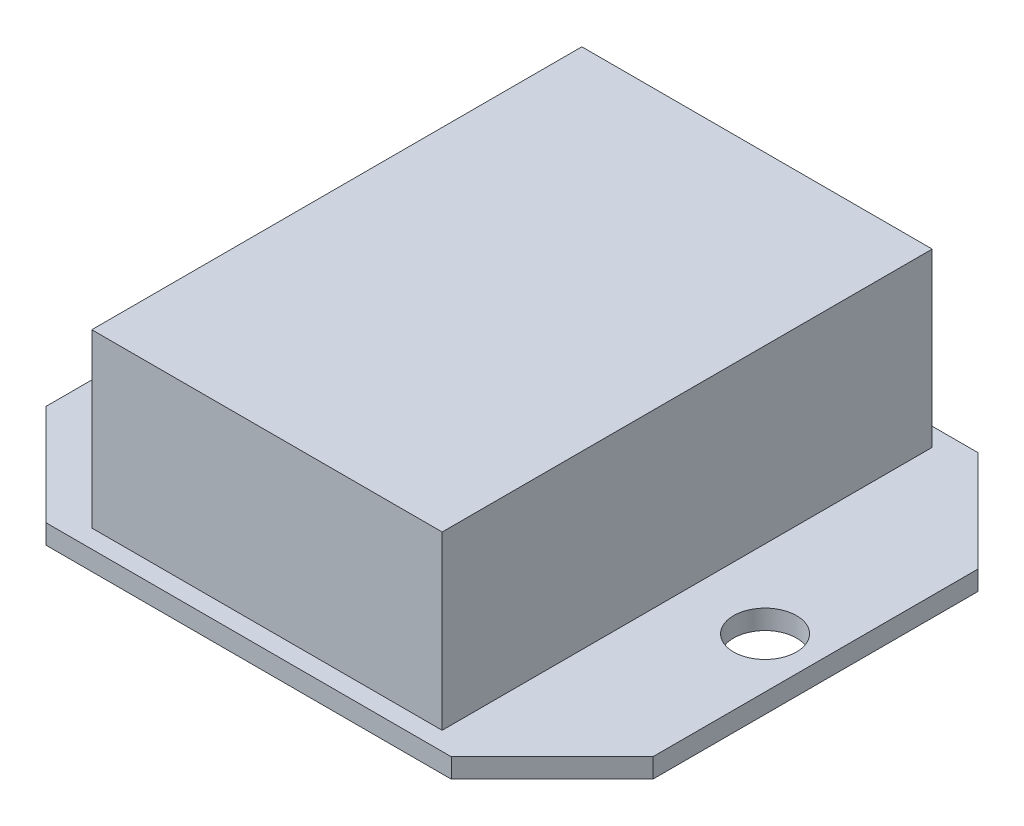
SolidWorks part; units mm, degrees
ref_plane "Front Plane" through (0, 0, 0) normal (0, 0, 1) x (1, 0, 0)
ref_plane "Top Plane" through (0, 0, 0) normal (0, 1, 0) x (1, 0, 0)
ref_plane "Right Plane" through (0, 0, 0) normal (1, 0, 0) x (0, 0, -1)
sketch "Sketch1" plane through (0, 0, 0) normal (0, 1, 0) x (1, 0, 0)
  line L1 (-33.655, 29.21) -> (33.655, 29.21)
  line L2 (-33.655, 29.21) -> (-33.655, -29.21)
  line L3 (-33.655, -29.21) -> (33.655, -29.21)
  line L4 (33.655, 29.21) -> (33.655, -29.21)
  line L5 (-33.655, 29.21) -> (33.655, -29.21) construction
  line L6 (-33.655, -29.21) -> (33.655, 29.21) construction
  point P0 (0, 0)
  dimension "D1" = 67.31
  dimension "D2" = 58.42
extrude "Boss-Extrude1" add sketch "Sketch1" along normal blind 2.159
sketch "Sketch2" plane through (0, 2.159, 0) normal (0, 1, 0) x (1, 0, 0)
  line L5 (33.655, 29.21) -> (-33.655, 29.21) construction
  line L6 (-19.431, 27.178) -> (19.431, 27.178)
  line L7 (-19.431, 27.178) -> (-19.431, -27.178)
  line L8 (-19.431, -27.178) -> (19.431, -27.178)
  line L9 (19.431, 27.178) -> (19.431, -27.178)
  line L10 (-19.431, 27.178) -> (19.431, -27.178) construction
  line L11 (-19.431, -27.178) -> (19.431, 27.178) construction
  point P0 (0, 0)
  point P1 (0, 0)
  dimension "D1" = 2.032
  dimension "D2" = 38.862
extrude "Boss-Extrude3" add sketch "Sketch2" along normal blind 19.05
sketch "Sketch3" plane through (0, 2.159, 0) normal (0, 1, 0) x (1, 0, 0)
  line L0 (33.655, -29.21) -> (33.655, 29.21) construction
  point P0 (28.067, 0)
  dimension "D1" = 5.588
sketch "Sketch4" plane through (0, 2.159, 0) normal (0, 1, 0) x (1, 0, 0)
  point P0 (28.067, 0)
hole_wizard "#97 (0.275) Diameter Hole1" positions "Sketch4" profile "Sketch5" hole size "#97" standard "ANSI Inch"
sketch "Sketch5" plane through (28.067, 2.159, 0) normal (1, 0, 0) x (0, 0, 1)
  line L0 (0, 0) -> (0, 6.1625)
  line L1 (0, 6.1625) -> (3.4925, 4.064)
  line L2 (3.4925, 4.064) -> (3.4925, 0)
  line L5 (3.4925, 0) -> (0, 0)
  line L10 (0, 6.1625) -> (-3.4925, 4.064) construction
  line L11 (0, -6.35) -> (0, 107.95) construction
  dimension "Hole Dia." = 6.985
  dimension "Hole Depth" = 4.064
  dimension "Drill Angle" = 118
mirror "Mirror1" about plane through (0, 0, 0) normal (1, 0, 0) of "#97 (0.275) Diameter Hole1"
chamfer "Chamfer1" distance 11.176 angle 45 4 edges at (-33.655, 1.0795, 29.21) (-33.655, 1.0795, -29.21) (33.655, 1.0795, -29.21) (33.655, 1.0795, 29.21)
